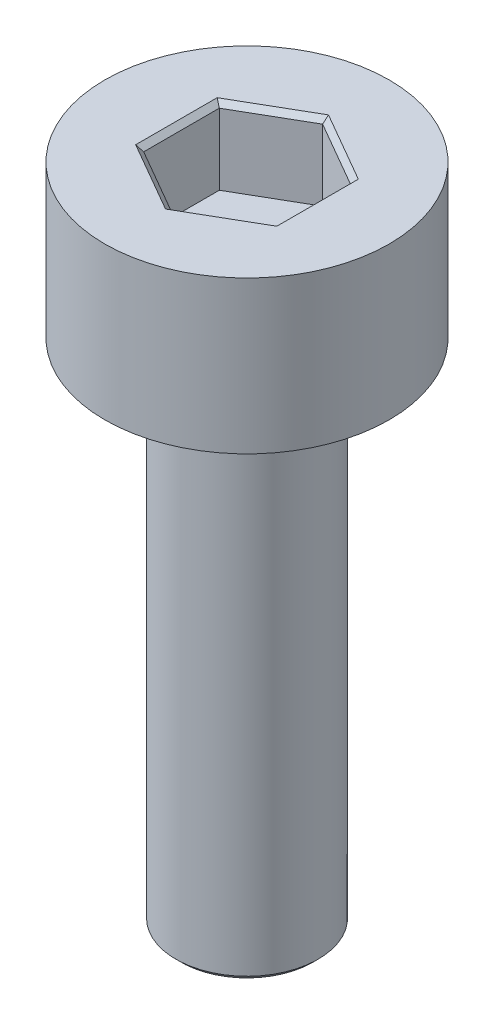
SolidWorks part; units mm, degrees
material "铸造合金钢"
ref_plane "前视基准面" through (0, 0, 0) normal (0, 0, 1) x (1, 0, 0)
ref_plane "上视基准面" through (0, 0, 0) normal (0, 1, 0) x (1, 0, 0)
ref_plane "右视基准面" through (0, 0, 0) normal (1, 0, 0) x (0, 0, -1)
sketch "草图1" plane through (0, 0, 0) normal (0, 1, 0) x (1, 0, 0)
  circle A0 centre (0, 0) radius 2.8
  dimension "D1" = 5.6
extrude "凸台-拉伸1" add sketch "草图1" along normal blind 3
sketch "草图2" plane through (0, 3, 0) normal (0, 1, 0) x (1, 0, 0)
  line L1 (0, -1.4896) -> (1.29, -0.7448)
  line L2 (1.29, -0.7448) -> (1.29, 0.7448)
  line L3 (1.29, 0.7448) -> (0, 1.4896)
  line L4 (0, 1.4896) -> (-1.29, 0.7448)
  line L5 (-1.29, 0.7448) -> (-1.29, -0.7448)
  line L6 (-1.29, -0.7448) -> (0, -1.4896)
  circle A0 centre (0, 0) radius 1.29 construction
  dimension "D1" = 2.58
extrude "切除-拉伸1" cut sketch "草图2" against normal blind 1.5
sketch "草图3" plane through (0, 0, 0) normal (0, -1, 0) x (1, 0, 0)
  circle A0 centre (0, 0) radius 1.4
  dimension "D1" = 2.8
extrude "凸台-拉伸2" add sketch "草图3" along normal blind 10
chamfer "倒角1" distance 0.1 angle 45 7 edges at (0.645, 3, -1.1172) (-0.645, 3, -1.1172) (-1.29, 3, 0) (-0.645, 3, 1.1172) (0.645, 3, 1.1172) (1.29, 3, 0) (0, -10, -1.4)
